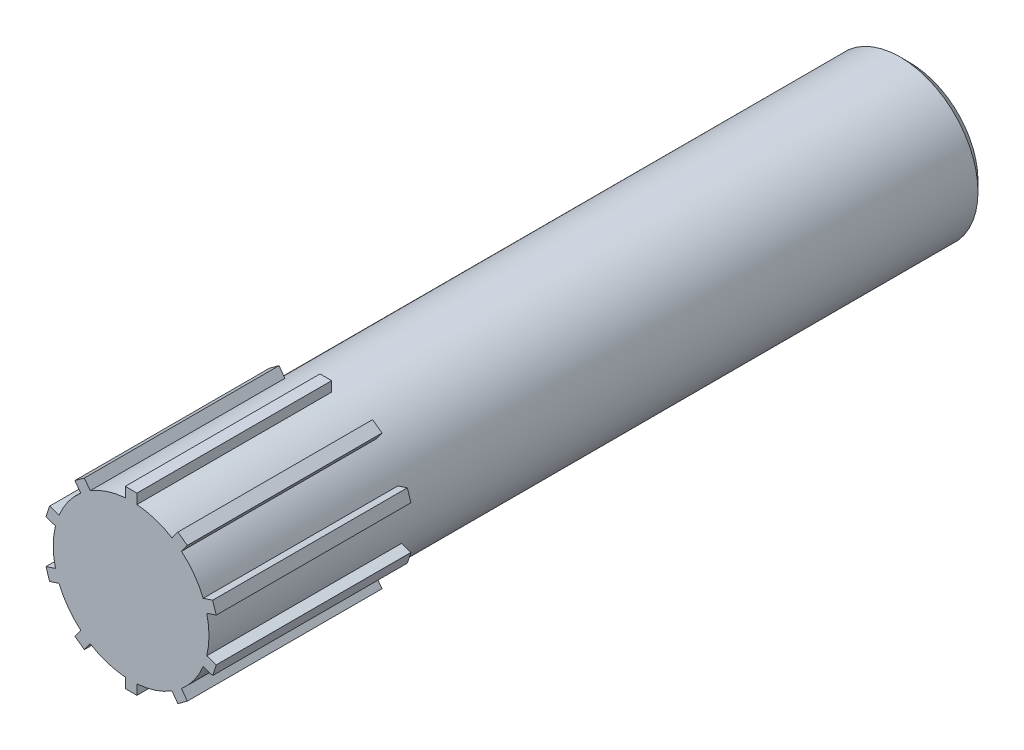
SolidWorks part; units mm, degrees
ref_plane "Front Plane" through (0, 0, 0) normal (0, 0, 1) x (1, 0, 0)
ref_plane "Top Plane" through (0, 0, 0) normal (0, 1, 0) x (1, 0, 0)
ref_plane "Right Plane" through (0, 0, 0) normal (1, 0, 0) x (0, 0, -1)
sketch "Sketch1" plane through (0, 0, 0) normal (0, 0, 1) x (1, 0, 0)
  circle A0 centre (0, 0) radius 4
  dimension "D1" = 8
extrude "Boss-Extrude1" add sketch "Sketch1" along normal blind 40
sketch "Sketch2" plane through (0, 0, 0) normal (0, 1, 0) x (1, 0, 0)
  line L0 (0, 0) -> (0, -40) construction
  line L1 (-4, -40) -> (4, -40) construction
  line L2 (0, -5) -> (0, -9) construction
  line L3 (1.5, -5) -> (1.5, -9)
  line L4 (-1.5, -5) -> (-1.5, -9)
  line L5 (4, 0) -> (-4, 0) construction
  arc A0 (1.5, -5) -> (-1.5, -5) centre (0, -5) ccw
  arc A1 (-1.5, -9) -> (1.5, -9) centre (0, -9) ccw
  point P7 (0, -7)
  dimension "D2" = 1.5
  dimension "D1" = 4
  dimension "D3" = 5
extrude "Cut-Extrude1" cut sketch "Sketch2" against normal through all from offset 2.5 offset against normal yes
sketch "Sketch3" plane through (0, 0, 40) normal (0, 0, 1) x (1, 0, 0)
  line L0 (0, 0) -> (0, 4) construction
  line L2 (0.3, 2.5364) -> (-0.3, 2.5364)
  line L3 (0.3, 2.5364) -> (0.3, 4.5)
  line L4 (0.3, 4.5) -> (-0.3, 4.5)
  line L5 (-0.3, 2.5364) -> (-0.3, 4.5)
  circle A0 centre (0, 0) radius 4 construction
  point P6 (0, 3.5182)
  point P11 (0, 0)
  point P12 (0, 0)
  dimension "D1" = 0.6
  dimension "D2" = 4.5
extrude "Boss-Extrude2" add sketch "Sketch3" against normal blind 10
pattern_circular "CirPattern1" count 10 over 360 about axis through (0, 0, 0) along (0, 0, 1) of "Boss-Extrude2"
chamfer "Chamfer1" distance 0.5 angle 45 1 edges at (4, 0, 0)
